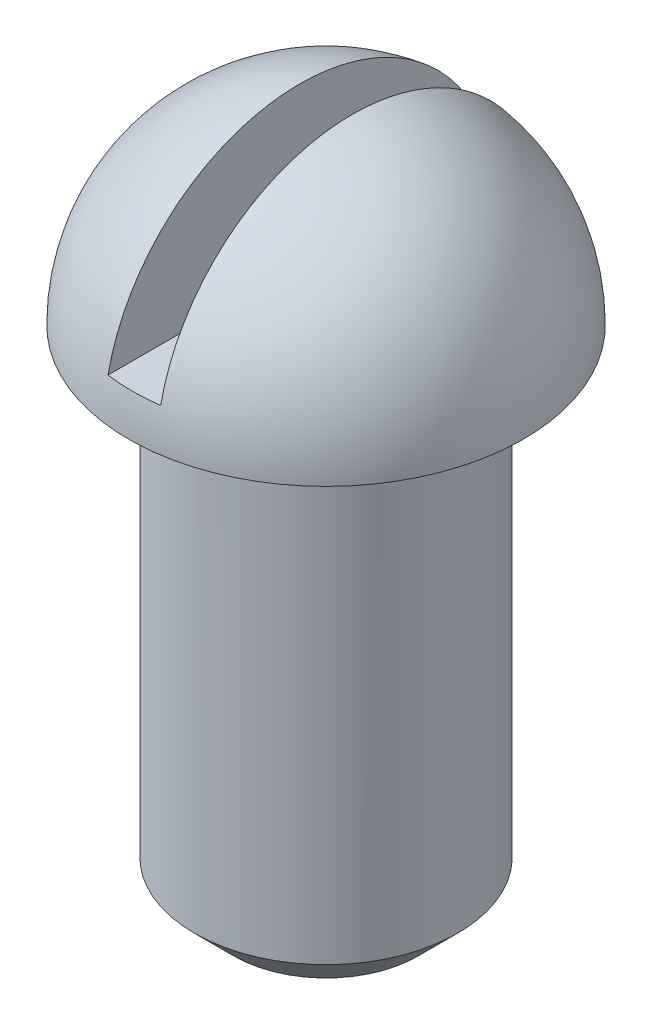
SolidWorks part; units mm, degrees
material "1060 Alloy"
ref_plane "Front Plane" through (0, 0, 0) normal (0, 0, 1) x (1, 0, 0)
ref_plane "Top Plane" through (0, 0, 0) normal (0, 1, 0) x (1, 0, 0)
ref_plane "Right Plane" through (0, 0, 0) normal (1, 0, 0) x (0, 0, -1)
sketch "Sketch4" plane through (0, 0, 0) normal (0, 0, 1) x (1, 0, 0)
  line L0 (10, -13.6595) -> (10, 85.5022) construction
  line L1 (0, 0) -> (10, 0)
  line L2 (0, 0) -> (0, 38)
  line L5 (0, 38) -> (-5, 38)
  line L6 (10, 0) -> (10, 53)
  arc A0 (10, 53) -> (-5, 38) centre (10, 38) ccw
  dimension "D3" = 15
  dimension "D1" = 38
  dimension "D2" = 10
  dimension "D4" = 53
  dimension "D5" = 15
  dimension "D6" = 10
revolve "Revolve1" add sketch "Sketch4" angle 360 about L0
sketch "Sketch6" plane through (0, 0, 0) normal (0, 0, 1) x (1, 0, 0)
  line L0 (10, 47) -> (10, 20) construction
  line L1 (8, 56) -> (12, 56)
  line L2 (8, 56) -> (8, 41)
  line L3 (8, 41) -> (12, 41)
  line L4 (12, 56) -> (12, 41)
  line L5 (0, 38) -> (20, 38) construction
  point P4 (10, 41)
  dimension "D1" = 3
  dimension "D2" = 4
  dimension "D3" = 15
extrude "Cut-Extrude1" cut sketch "Sketch6" against normal mid plane 55
chamfer "Chamfer1" distance 3 angle 45 1 edges at (10, 0, -10)
